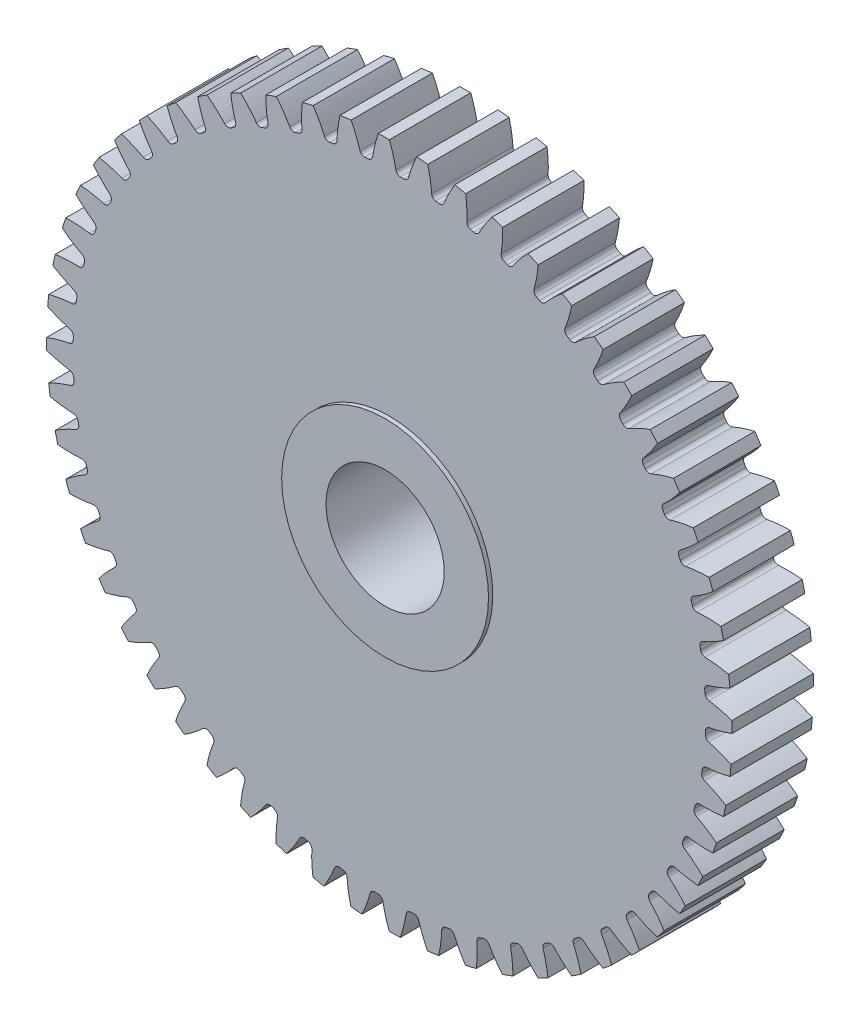
SolidWorks part; units mm, degrees
ref_plane "Front" through (0, 0, 0) normal (0, 0, 1) x (1, 0, 0)
ref_plane "Top" through (0, 0, 0) normal (0, 1, 0) x (1, 0, 0)
ref_plane "Right" through (0, 0, 0) normal (1, 0, 0) x (0, 0, -1)
sketch "Sketch3" plane through (0, 0, 0) normal (0, 0, 1) x (1, 0, 0)
  circle A0 centre (0, 0) radius 36.83
  dimension "od" = 73.66
extrude "gearBody" add sketch "Sketch3" along normal blind 8.7376
sketch "Sketch2" plane through (0, 0, 0) normal (0, 0, 1) x (1, 0, 0)
  line L0 (0, 0) -> (31.8067, 13.1748) construction
  line L1 (42.9048, -8.6911) -> (0, 0) construction
  line L2 (0, 0) -> (36.3143, 0) construction
  line L3 (35.5574, -0.4275) -> (35.4773, -2.4239) construction
  line L5 (35.5174, -1.4257) -> (0, 0) construction
  line L7 (0, 0) -> (34.4273, 0) construction
  arc A0 (34.4204, -0.6909) -> (34.365, -2.0702) centre (0, 0) ccw construction
  arc A1 (36.83, -0.0107) -> (36.7124, -2.9414) centre (0, 0) ccw construction
  arc A2 (35.5574, -0.4275) -> (35.4773, -2.4239) centre (0, 0) ccw construction
  arc A3 (33.9497, -1.5528) -> (33.9649, -1.1733) centre (0, 0) ccw
  arc A4 (42.9048, -8.6911) -> (34.3185, -2.0575) centre (30.6484, -15.6818) ccw
  arc A5 (42.9048, -8.6911) -> (43.4634, 5.2242) centre (0, 0) ccw
  arc A6 (43.4634, 5.2242) -> (34.373, -0.6998) centre (31.8067, 13.1748) cw
  arc A7 (33.9649, -1.1733) -> (34.373, -0.6998) centre (34.4638, -1.1906) cw
  arc A8 (34.3185, -2.0575) -> (33.9497, -1.5528) centre (34.4483, -1.5756) cw
  point P6 (43.4634, 5.2242)
  point P22 (42.9048, -8.6911)
  dimension "baseDia" = 68.8547
  dimension "od" = 73.66
  dimension "pd" = 71.12
  dimension "rd" = 67.9704
  dimension "rFillet" = 0.4991
  dimension "pointX" = 43.4634
  dimension "pointY" = 5.2242
  dimension "CTT" = 1.9964
  dimension "flankCenterAngle" = 22.5
extrude "toothCut" cut sketch "Sketch2" along normal through all
pattern_circular "CirPattern1" count 56 over 360 about axis through (0, 0, 0) along (0, 0, 1) of "toothCut"
sketch "hub1Dia" plane through (0, 0, 0) normal (0, 0, -1) x (-1, 0, 0)
  circle A0 centre (0, 0) radius 25.4
  dimension "hub1Dia" = 50.8
extrude "hub1" [suppressed] add sketch "hub1Dia" along normal blind 19.05
sketch "hub2Dia" plane through (0, 0, 8.7376) normal (0, 0, 1) x (1, 0, 0)
  circle A0 centre (0, 0) radius 21.844
  dimension "hub2dia" = 43.688
extrude "hub2" [suppressed] add sketch "hub2Dia" along normal blind 16.002
sketch "boreDia" plane through (0, 0, 0) normal (0, 0, 1) x (1, 0, 0)
  circle A0 centre (0, 0) radius 6.35
  dimension "boreDia" = 12.7
extrude "bore" cut sketch "boreDia" against normal mid plane 25400
chamfer "hub2Chamfer" [suppressed] distance 0.508 angle 45
chamfer "hub2BoreChamfer" [suppressed] distance 0.508 angle 45
chamfer "hub1BoreChamfer" [suppressed] distance 0.508 angle 45
chamfer "hub1Chamfer" [suppressed] distance 0.508 angle 45
chamfer "BoreChamfer2" [suppressed] distance 0.508 angle 45
chamfer "boreChamfer1" [suppressed] distance 0.508 angle 45
sketch "Sketch4" plane through (0, 0, 0) normal (0, 0, -1) x (-1, 0, 0)
  circle A0 centre (0, 0) radius 11.1125
  circle A1 centre (0, 0) radius 6.35
  dimension "D1" = 22.225
extrude "Boss-Extrude1" add sketch "Sketch4" along normal blind 0.4572
sketch "Sketch5" plane through (0, 0, 8.7376) normal (0, 0, 1) x (1, 0, 0)
  circle A0 centre (0, 0) radius 6.35
  circle A1 centre (0, 0) radius 11.1125
  dimension "D1" = 22.225
extrude "Boss-Extrude2" add sketch "Sketch5" along normal blind 0.4572
